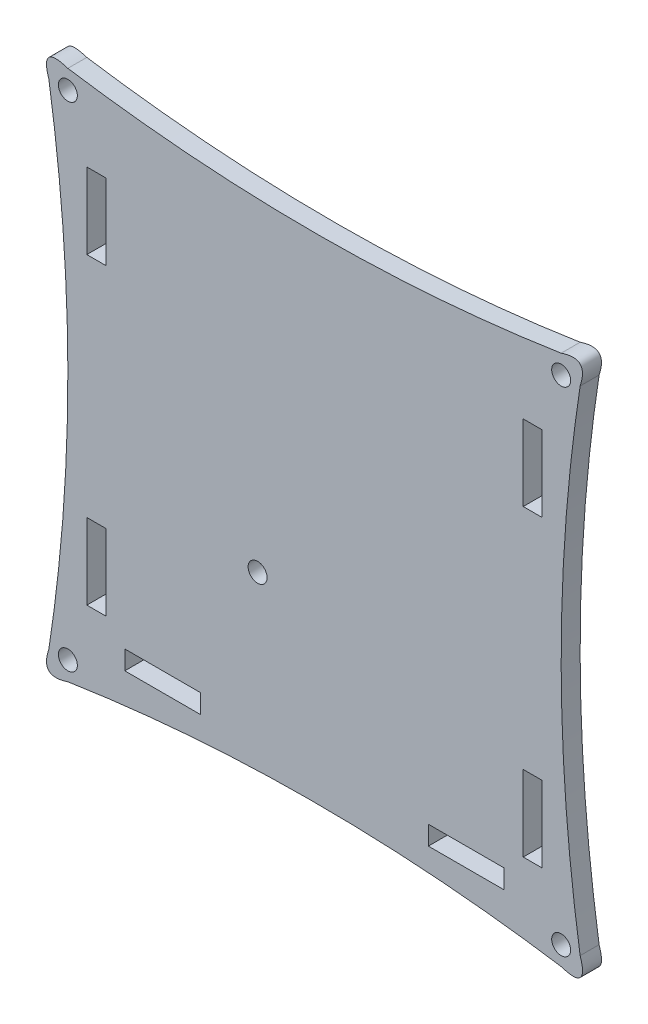
SolidWorks part; units mm, degrees
ref_plane "Front Plane" through (0, 0, 0) normal (0, 0, 1) x (1, 0, 0)
ref_plane "Top Plane" through (0, 0, 0) normal (0, 1, 0) x (1, 0, 0)
ref_plane "Right Plane" through (0, 0, 0) normal (1, 0, 0) x (0, 0, -1)
sketch "Sketch1" plane through (0, 0, 0) normal (0, 0, 1) x (1, 0, 0)
  line L0 (12.7, 50.8) -> (19.05, 50.8)
  line L1 (25.4, 19.05) -> (50.8, 19.05)
  line L2 (12.7, 152.4) -> (12.7, 127)
  line L3 (25.4, 12.7) -> (50.8, 12.7)
  line L4 (19.05, 152.4) -> (19.05, 127)
  line L5 (12.7, 25.4) -> (19.05, 25.4)
  line L6 (12.7, 152.4) -> (19.05, 152.4)
  line L7 (12.7, 127) -> (19.05, 127)
  line L8 (165.1, 152.4) -> (158.75, 152.4)
  line L9 (127, 19.05) -> (152.4, 19.05)
  line L10 (19.05, 50.8) -> (19.05, 25.4)
  line L11 (127, 12.7) -> (152.4, 12.7)
  line L12 (12.7, 50.8) -> (12.7, 25.4)
  line L13 (165.1, 127) -> (158.75, 127)
  line L14 (158.75, 50.8) -> (165.1, 50.8)
  line L15 (158.75, 25.4) -> (165.1, 25.4)
  line L16 (165.1, 152.4) -> (165.1, 127)
  line L17 (158.75, 152.4) -> (158.75, 127)
  line L18 (158.75, 50.8) -> (158.75, 25.4)
  line L19 (165.1, 50.8) -> (165.1, 25.4)
  line L20 (25.4, 12.7) -> (25.4, 19.05)
  line L21 (50.8, 19.05) -> (50.8, 12.7)
  line L22 (152.4, 19.05) -> (152.4, 12.7)
  line L23 (127, 19.05) -> (127, 12.7)
  spline S0 degree 2 poles (0, 171.45) (12.7, 88.9) (0, 6.35) knots 0 0 0 1 1 1
  spline S1 degree 2 poles (0, 171.45) (-3.175, 180.975) (6.35, 177.8) knots 0 0 0 1 1 1
  spline S2 degree 2 poles (6.35, 177.8) (88.9, 165.1) (171.45, 177.8) knots 0 0 0 1 1 1
  spline S3 degree 2 poles (171.45, 177.8) (180.975, 180.975) (177.8, 171.45) knots 0 0 0 1 1 1
  spline S4 degree 2 poles (177.8, 171.45) (165.1, 88.9) (177.8, 6.35) knots 0 0 0 1 1 1
  spline S5 degree 2 poles (177.8, 6.35) (180.975, -3.175) (171.45, 0) knots 0 0 0 1 1 1
  spline S6 degree 2 poles (0, 6.35) (-3.175, -3.175) (6.35, 0) knots 0 0 0 1 1 1
  spline S7 degree 2 poles (6.35, 0) (88.9, 12.7) (171.45, 0) knots 0 0 0 1 1 1
extrude "Boss-Extrude1" add sketch "Sketch1" along normal blind 6.35
sketch "Sketch2" plane through (0, 0, 6.35) normal (0, 0, 1) x (1, 0, 0)
  circle A0 centre (69.85, 63.5) radius 3.175
extrude "Cut-Extrude1" cut sketch "Sketch2" against normal blind 6.35
sketch "Sketch3" plane through (0, 0, 6.35) normal (0, 0, 1) x (1, 0, 0)
  circle A0 centre (6.35, 6.35) radius 3.175
  circle A1 centre (171.45, 6.35) radius 3.175
  circle A2 centre (171.45, 171.45) radius 3.175
  circle A3 centre (6.35, 171.45) radius 3.175
extrude "Cut-Extrude2" cut sketch "Sketch3" against normal blind 6.35
